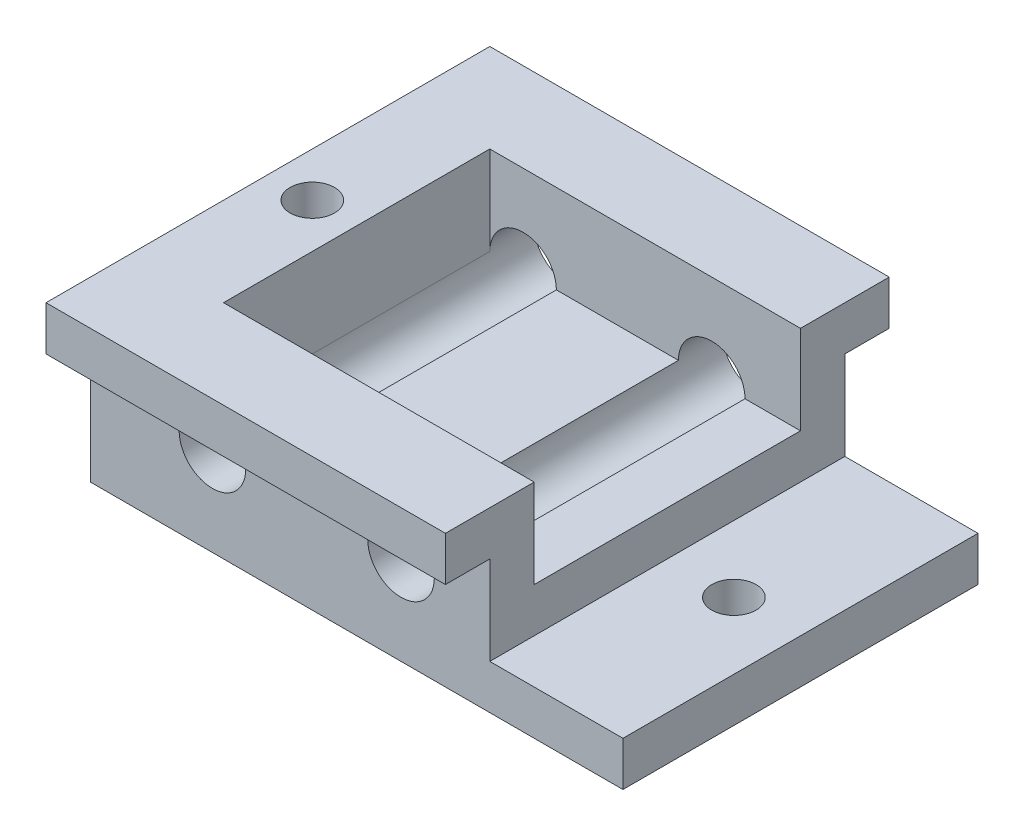
SolidWorks part; units mm, degrees
ref_plane "Front Plane" through (0, 0, 0) normal (0, 0, 1) x (1, 0, 0)
ref_plane "Top Plane" through (0, 0, 0) normal (0, 1, 0) x (1, 0, 0)
ref_plane "Right Plane" through (0, 0, 0) normal (1, 0, 0) x (0, 0, -1)
sketch "Sketch1" plane through (0, 0, 0) normal (0, 1, 0) x (1, 0, 0)
  line L0 (-38.1, 25.4) -> (38.1, -25.4) construction
  line L1 (-38.1, -25.4) -> (38.1, -25.4)
  line L2 (-38.1, -25.4) -> (-38.1, 25.4)
  line L3 (-38.1, 25.4) -> (38.1, 25.4)
  line L4 (38.1, -25.4) -> (38.1, 25.4)
  dimension "D1" = 50.8
  dimension "D2" = 76.2
extrude "Boss-Extrude1" add sketch "Sketch1" along normal blind 6.35
sketch "Sketch2" plane through (0, 6.35, 0) normal (0, 1, 0) x (1, 0, 0)
  line L1 (-38.1, 25.4) -> (19.05, 25.4)
  line L2 (-38.1, 25.4) -> (-38.1, -25.4)
  line L3 (-38.1, -25.4) -> (19.05, -25.4)
  line L4 (19.05, 25.4) -> (19.05, -25.4)
  line L6 (-38.1, -25.4) -> (38.1, -25.4) construction
  dimension "D1" = 57.15
extrude "Boss-Extrude2" add sketch "Sketch2" along normal blind 6.35
sketch "Sketch3" plane through (0, 12.7, 0) normal (0, 1, 0) x (1, 0, 0)
  line L0 (19.05, 25.4) -> (-38.1, 25.4)
  line L1 (-38.1, 25.4) -> (-38.1, -25.4)
  line L2 (-38.1, 25.4) -> (-38.1, -25.4) construction
  line L3 (-38.1, -25.4) -> (19.05, -25.4)
  line L4 (19.05, -25.4) -> (19.05, -19.05)
  line L5 (19.05, -25.4) -> (19.05, 25.4) construction
  line L6 (19.05, -19.05) -> (-25.4, -19.05)
  line L7 (-25.4, -19.05) -> (-25.4, 19.05)
  line L8 (-25.4, 19.05) -> (19.05, 19.05)
  line L9 (19.05, 19.05) -> (19.05, 25.4)
  dimension "D1" = 6.35
  dimension "D2" = 12.7
extrude "Boss-Extrude3" add sketch "Sketch3" along normal blind 6.35
sketch "Sketch4" plane through (0, 19.05, 0) normal (0, 1, 0) x (1, 0, 0)
  line L0 (19.05, 19.05) -> (19.05, 31.75)
  line L1 (19.05, 31.75) -> (-38.1, 31.75)
  line L2 (-38.1, 31.75) -> (-38.1, -31.75)
  line L3 (-38.1, -31.75) -> (19.05, -31.75)
  line L4 (19.05, -31.75) -> (19.05, -19.05)
  line L5 (19.05, -19.05) -> (-25.4, -19.05)
  line L6 (-25.4, -19.05) -> (-25.4, 19.05)
  line L7 (-25.4, 19.05) -> (19.05, 19.05)
  dimension "D1" = 12.7
extrude "Boss-Extrude4" add sketch "Sketch4" along normal blind 6.35
sketch "Sketch5" plane through (0, 0, 0) normal (0, 1, 0) x (1, 0, 0)
  line L0 (-38.1, 31.75) -> (-38.1, -31.75) construction
  line L1 (38.1, -25.4) -> (38.1, 25.4) construction
  circle A0 centre (-31.75, 0) radius 3.175
  circle A1 centre (28.575, 0) radius 3.175
  dimension "D1" = 6.35
  dimension "D2" = 6.35
  dimension "D3" = 9.525
extrude "Cut-Extrude1" cut sketch "Sketch5" along normal through all
sketch "Sketch6" plane through (0, 0, 0) normal (0, 0, 1) x (1, 0, 0)
  line L0 (19.05, 12.7) -> (-25.4, 12.7) construction
  line L1 (-38.1, 19.05) -> (-38.1, 0) construction
  line L2 (-25.4, 25.4) -> (-25.4, 12.7) construction
  circle A0 centre (-20.6375, 12.7) radius 4.7625
  circle A1 centre (6.35, 12.7) radius 4.7625
  dimension "D1" = 9.525
  dimension "D3" = 44.45
extrude "Cut-Extrude2" cut sketch "Sketch6" against normal through all both and the other way through all
